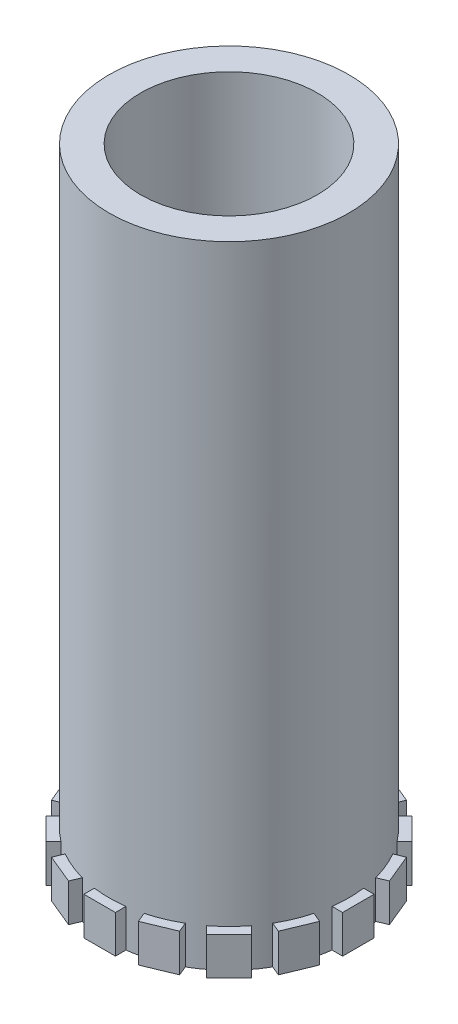
SolidWorks part; units mm, degrees
material "ABS"
ref_plane "前视基准面" through (0, 0, 0) normal (0, 0, 1) x (1, 0, 0)
ref_plane "上视基准面" through (0, 0, 0) normal (0, 1, 0) x (1, 0, 0)
ref_plane "右视基准面" through (0, 0, 0) normal (1, 0, 0) x (0, 0, -1)
sketch "草图1" plane through (0, 0, 0) normal (0, 1, 0) x (1, 0, 0)
  circle A0 centre (0, 0) radius 9.5
  circle A1 centre (0, 0) radius 7
  dimension "D1" = 19
  dimension "D2" = 14
extrude "凸台-拉伸1" add sketch "草图1" along normal blind 50
sketch "草图2" plane through (0, 0, 0) normal (0, -1, 0) x (-1, 0, 0)
  line L1 (10.25, -1.25) -> (8.75, -1.25)
  line L2 (10.25, -1.25) -> (10.25, 1.25)
  line L3 (10.25, 1.25) -> (8.75, 1.25)
  line L4 (8.75, -1.25) -> (8.75, 1.25)
  line L5 (10.25, -1.25) -> (8.75, 1.25) construction
  line L6 (10.25, 1.25) -> (8.75, -1.25) construction
  circle A0 centre (0, 0) radius 9.5 construction
  point P0 (9.5, 0)
  dimension "D1" = 1.5
  dimension "D2" = 2.5
extrude "凸台-拉伸2" add sketch "草图2" against normal blind 3
pattern_circular "阵列(圆周)1" count 16 over 360 about axis through (0, 0, 0) along (0, 1, 0) of "凸台-拉伸2"
